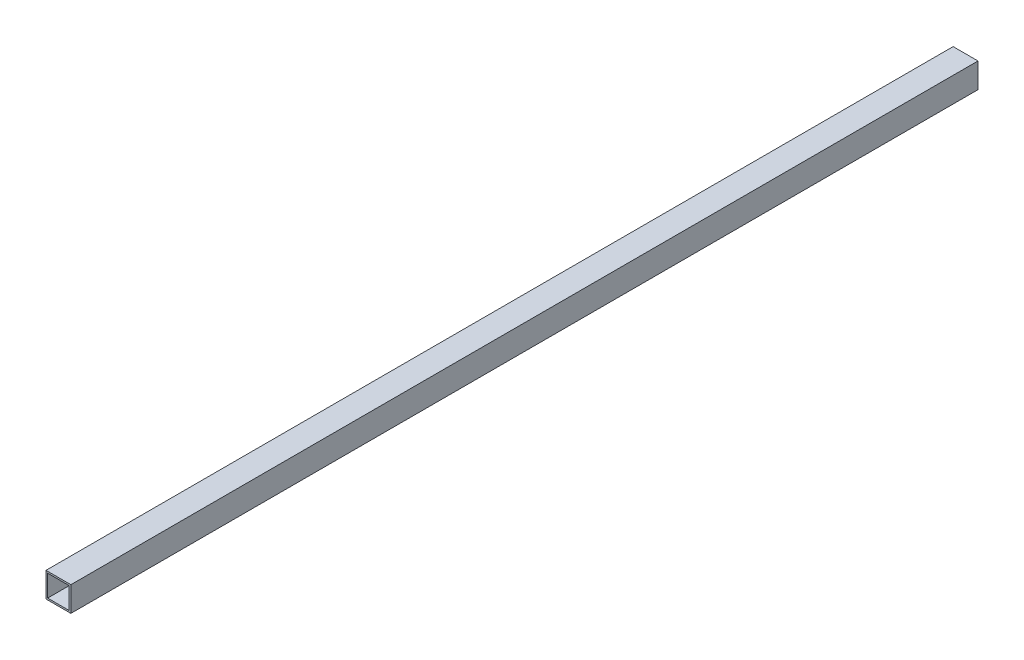
SolidWorks part; units mm, degrees
ref_plane "Front Plane" through (0, 0, 0) normal (0, 0, 1) x (1, 0, 0)
ref_plane "Top Plane" through (0, 0, 0) normal (0, 1, 0) x (1, 0, 0)
ref_plane "Right Plane" through (0, 0, 0) normal (1, 0, 0) x (0, 0, -1)
curve "Curve1"
  spline degree 1 poles (0, 0, 0) (0, 0, 2188) knots 0 0 1 1
sketch "Sketch1" plane through (0, 0, 0) normal (0, 0, 1) x (1, 0, 0)
  line L0 (0, 35.3535) -> (0, -33.8384) construction
  line L1 (-30, 30) -> (30, 30)
  line L2 (-30, 30) -> (-30, -30)
  line L3 (-30, -30) -> (30, -30)
  line L4 (30, 30) -> (30, -30)
  line L5 (-26, 26) -> (26, 26)
  line L6 (-26, 26) -> (-26, -26)
  line L7 (-26, -26) -> (26, -26)
  line L8 (26, 26) -> (26, -26)
  line L9 (-39.3939, 0) -> (41.5152, 0) construction
  dimension "D1" = 60
  dimension "D2" = 52
sweep "Sweep1" add profiles "Sketch1" path "Curve1"
